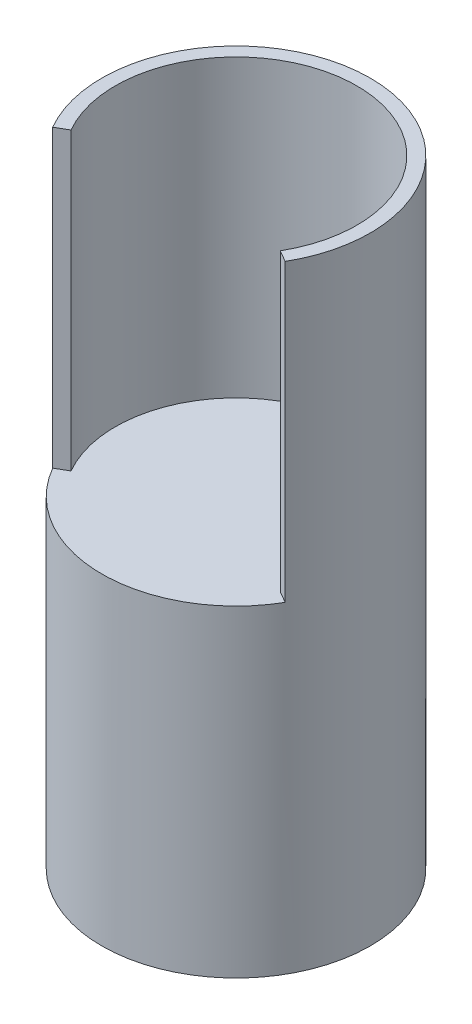
SolidWorks part; units mm, degrees
ref_plane "Front Plane" through (0, 0, 0) normal (0, 0, 1) x (1, 0, 0)
ref_plane "Top Plane" through (0, 0, 0) normal (0, 1, 0) x (1, 0, 0)
ref_plane "Right Plane" through (0, 0, 0) normal (1, 0, 0) x (0, 0, -1)
sketch "Sketch1" plane through (0, 0, 0) normal (0, 1, 0) x (1, 0, 0)
  circle A0 centre (0, 0) radius 63.5
  dimension "D1" = 127
extrude "Boss-Extrude1" add sketch "Sketch1" along normal blind 152.4
sketch "Sketch3" plane through (0, 152.4, 0) normal (0, 1, 0) x (1, 0, 0)
  line L0 (-54.9926, -31.75) -> (-49.4934, -28.575)
  line L1 (49.4934, -28.575) -> (54.9926, -31.75)
  line L2 (0, 0) -> (0, 63.5) construction
  arc A0 (-54.9926, -31.75) -> (54.9926, -31.75) centre (0, 0) cw
  circle A1 centre (0, 0) radius 63.5 construction
  arc A2 (-49.4934, -28.575) -> (49.4934, -28.575) centre (0, 0) cw
  dimension "D1" = 57.15
  dimension "D2" = 120
  dimension "D3" = 120
extrude "Boss-Extrude2" add sketch "Sketch3" along normal blind 139.7
